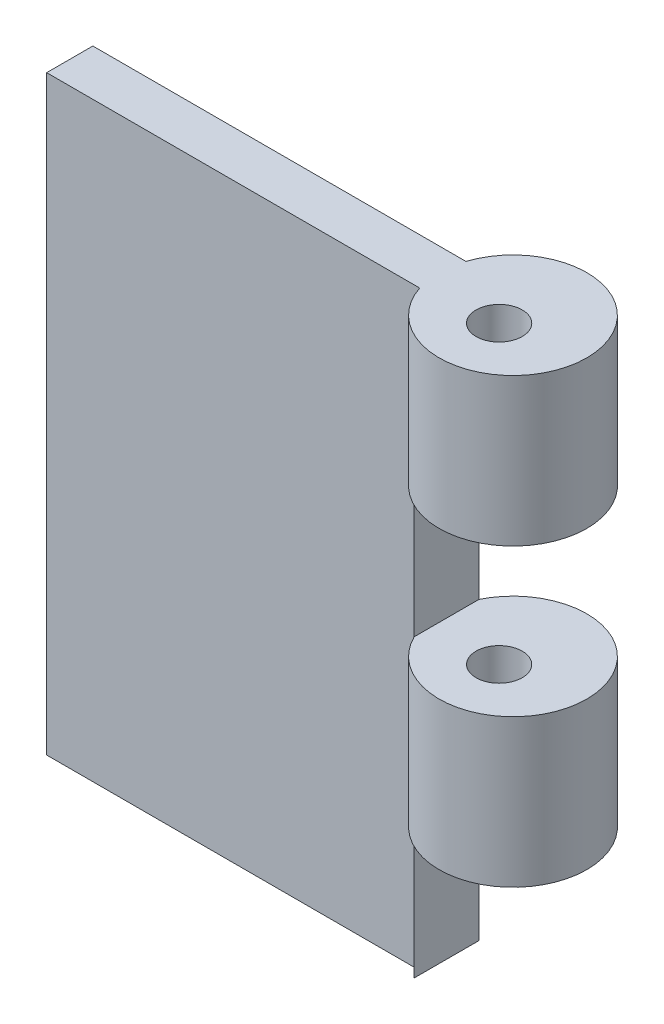
SolidWorks part; units mm, degrees
ref_plane "Front Plane" through (0, 0, 0) normal (0, 0, 1) x (1, 0, 0)
ref_plane "Top Plane" through (0, 0, 0) normal (0, 1, 0) x (1, 0, 0)
ref_plane "Right Plane" through (0, 0, 0) normal (1, 0, 0) x (0, 0, -1)
sketch "Sketch1" plane through (0, 0, 0) normal (0, 0, 1) x (1, 0, 0)
  line L1 (-7.62, -10.16) -> (7.62, -10.16)
  line L2 (-7.62, -10.16) -> (-7.62, 10.16)
  line L3 (-7.62, 10.16) -> (7.62, 10.16)
  line L4 (7.62, -10.16) -> (7.62, 10.16)
  line L5 (-7.62, -10.16) -> (7.62, 10.16) construction
  line L6 (-7.62, 10.16) -> (7.62, -10.16) construction
  point P0 (0, 0)
  dimension "D1" = 20.32
  dimension "D2" = 15.24
extrude "Boss-Extrude1" add sketch "Sketch1" along normal blind 1.5875
sketch "Sketch2" plane through (7.62, 0, 0) normal (1, 0, 0) x (0, 0, -1)
  line L0 (-0.7937, -10.16) -> (-0.7937, 10.16)
  line L1 (-1.5875, -10.16) -> (0, -10.16) construction
  line L2 (-1.5875, 10.16) -> (0, 10.16) construction
revolve "Revolve-Thin1" add sketch "Sketch2" angle 360 about L0 wall 2.54
sketch "Sketch7" plane through (0, 10.16, 0) normal (0, 1, 0) x (1, 0, 0)
  circle A0 centre (7.62, -1.27) radius 2.54 construction
hole_wizard "1/16 (0.0625) Diameter Hole1" positions "Sketch9" profile "Sketch8" hole size "1/16" standard "ANSI Inch" end condition through all
sketch "Sketch9" plane through (0, 10.16, 0) normal (0, 1, 0) x (1, 0, 0)
  point P0 (7.62, -1.27)
sketch "Sketch8" plane through (7.62, 10.16, 1.27) normal (1, 0, 0) x (0, 0, 1)
  line L0 (0, 0) -> (0, 20.32)
  line L1 (0, 20.32) -> (0.7937, 20.32)
  line L2 (0.7937, 20.32) -> (0.7937, 0)
  line L5 (0.7937, 0) -> (0, 0)
  line L11 (0, -6.35) -> (0, 107.95) construction
  dimension "Thru Hole Dia." = 1.5875
  dimension "Thru Hole Depth" = 20.32
sketch "Sketch10" plane through (0, 0, 1.5875) normal (0, 0, 1) x (1, 0, 0)
  line L0 (0, 0) -> (10.935, 0) construction
  line L1 (5.4675, 0) -> (5.2072, 10.16) construction
  line L2 (5.4675, 0) -> (5.2072, -10.16) construction
  line L3 (5.3374, 5.08) -> (0, 5.08) construction
  line L4 (5.3374, -5.08) -> (0, -5.08) construction
  line L6 (5.3374, 5.08) -> (10.5828, 5.08)
  line L7 (5.3374, 5.08) -> (5.3374, 0)
  line L8 (5.3374, 0) -> (10.5828, 0)
  line L9 (10.5828, 5.08) -> (10.5828, 0)
  line L10 (5.3374, -5.08) -> (10.5828, -5.08)
  line L11 (5.3374, -5.08) -> (5.3374, -10.16)
  line L12 (5.3374, -10.16) -> (10.5828, -10.16)
  line L13 (10.5828, -5.08) -> (10.5828, -10.16)
extrude "Cut-Extrude1" cut sketch "Sketch10" against normal mid plane 12.7
